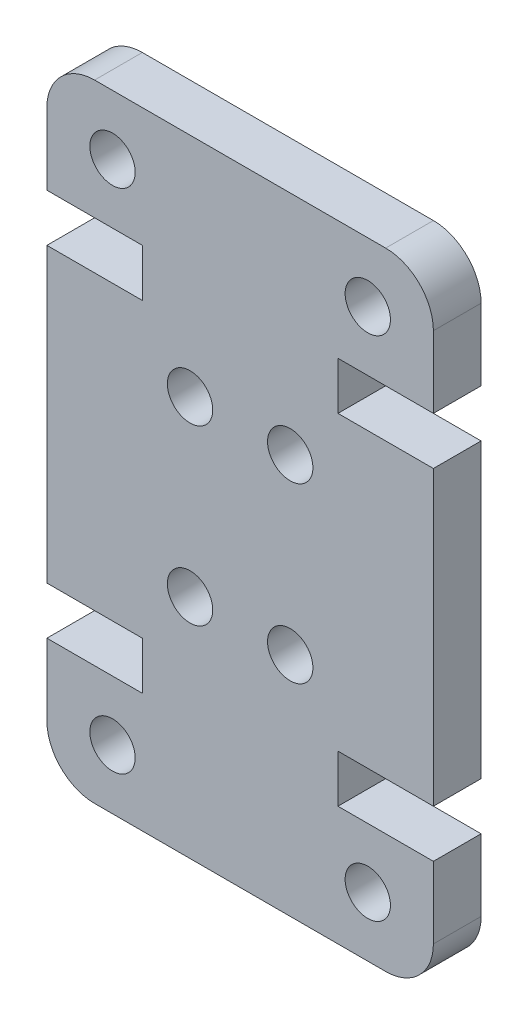
SolidWorks part; units mm, degrees
ref_plane "Front Plane" through (0, 0, 0) normal (0, 0, 1) x (1, 0, 0)
ref_plane "Top Plane" through (0, 0, 0) normal (0, 1, 0) x (1, 0, 0)
ref_plane "Right Plane" through (0, 0, 0) normal (1, 0, 0) x (0, 0, -1)
sketch "Sketch2" plane through (0, 0, 0) normal (0, 0, 1) x (1, 0, 0)
  line L0 (0, 13.13) -> (16.2, 13.13) construction
  line L1 (8.1, 26.26) -> (8.1, 0) construction
  line L2 (0, 7) -> (0, 19.26)
  line L3 (2, 0) -> (14.2, 0)
  line L4 (16.2, 2) -> (16.2, 5)
  line L5 (12.2, 5) -> (16.2, 5)
  line L6 (16.2, 7) -> (12.2, 7)
  line L7 (12.2, 7) -> (12.2, 5)
  line L8 (16.2, 7) -> (16.2, 19.26)
  line L9 (0, 24.26) -> (0, 21.26)
  line L10 (4, 21.26) -> (0, 21.26)
  line L11 (0, 19.26) -> (4, 19.26)
  line L12 (4, 19.26) -> (4, 21.26)
  line L13 (12.2, 19.26) -> (12.2, 21.26)
  line L14 (16.2, 19.26) -> (12.2, 19.26)
  line L15 (12.2, 21.26) -> (16.2, 21.26)
  line L16 (16.2, 24.26) -> (16.2, 21.26)
  line L17 (2, 26.26) -> (14.2, 26.26)
  line L27 (4, 7) -> (4, 5)
  line L30 (0, 7) -> (4, 7)
  line L32 (4, 5) -> (0, 5)
  line L36 (0, 2) -> (0, 5)
  circle A0 centre (13.45, 2.5) radius 0.95
  circle A1 centre (10.2, 9.5) radius 0.95
  arc A2 (16.2, 2) -> (14.2, 0) centre (14.2, 2) cw
  circle A3 centre (2.75, 23.76) radius 0.95
  circle A4 centre (6, 16.76) radius 0.95
  arc A5 (0, 24.26) -> (2, 26.26) centre (2, 24.26) cw
  arc A6 (16.2, 24.26) -> (14.2, 26.26) centre (14.2, 24.26) ccw
  circle A7 centre (10.2, 16.76) radius 0.95
  circle A8 centre (13.45, 23.76) radius 0.95
  arc A17 (0, 2) -> (2, 0) centre (2, 2) ccw
  circle A19 centre (6, 9.5) radius 0.95
  circle A21 centre (2.75, 2.5) radius 0.95
  point P16 (8.1, 13.13)
  dimension "D1" = 1.9
  dimension "D2" = 2
  dimension "D3" = 2.75
  dimension "D4" = 6
  dimension "D5" = 8.1
  dimension "D6" = 2.5
  dimension "D7" = 5
  dimension "D9" = 9.5
  dimension "D10" = 13.13
extrude "Boss-Extrude1" add sketch "Sketch2" along normal blind 4
sketch "Sketch3" plane through (0, 0, 4) normal (0, 0, 1) x (1, 0, 0)
  line L0 (0, 0) -> (0, 26.26)
  line L1 (0, 26.26) -> (16.2, 26.26)
  line L2 (16.2, 26.26) -> (16.2, 0)
  line L3 (16.2, 0) -> (0, 0)
extrude "Cut-Extrude1" cut sketch "Sketch3" against normal blind 2
equation "\"D5@Sketch2\"= \"fingerWidth@parametersSketch@prostheticParameters.SLDPRT\" / 2'Finger Width"
equation "\"D10@Sketch2\"= ( ( \"HL@parametersSketch@prostheticParameters.SLDPRT\" * 0.196 ) - 4 - 6 ) / 2 'PIP Length"
equation "\"D1@Sketch2\"= 1.5 + \"tol1@parametersSketch@prostheticParameters.SLDPRT\""
